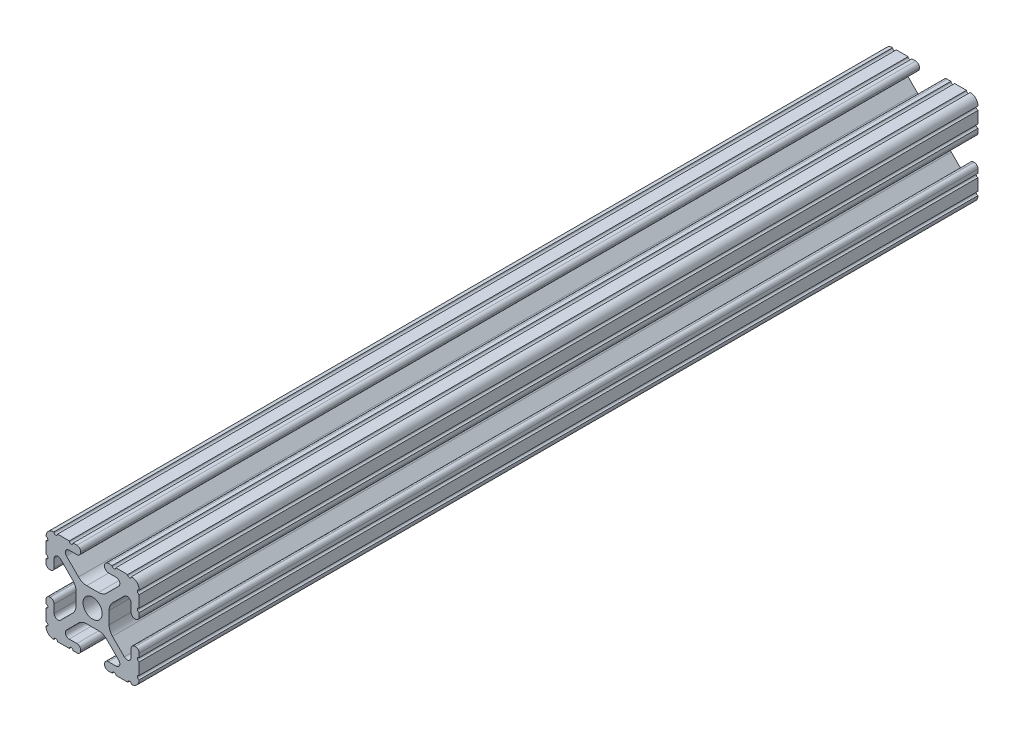
SolidWorks part; units mm, degrees
material "6061-T6 (SS)"
ref_plane "Front Plane" through (0, 0, 0) normal (0, 0, 1) x (1, 0, 0)
ref_plane "Top Plane" through (0, 0, 0) normal (0, 1, 0) x (1, 0, 0)
ref_plane "Right Plane" through (0, 0, 0) normal (1, 0, 0) x (0, 0, -1)
sketch "Sketch1" plane through (0, 0, 0) normal (0, 0, 1) x (0, 1, 0)
  line L0 (6.3331, -12.7) -> (9.5504, -12.7)
  line L1 (12.7, -9.5504) -> (12.7, -6.3331)
  line L2 (12.7, -5.3171) -> (12.7, -4.2875)
  line L3 (11.651, -3.2385) -> (11.5392, -3.2385)
  line L4 (10.4902, -4.2875) -> (10.4902, -6.4021)
  line L5 (8.7371, -7.1294) -> (5.441, -3.8408)
  line L6 (4.5085, -1.5932) -> (4.5085, 1.5932)
  line L7 (5.441, 3.8408) -> (8.7371, 7.1294)
  line L8 (10.4902, 6.4021) -> (10.4902, 4.2875)
  line L9 (11.5392, 3.2385) -> (11.651, 3.2385)
  line L10 (12.7, 4.2875) -> (12.7, 5.3171)
  line L11 (12.7, 6.3331) -> (12.7, 9.5504)
  line L12 (9.5504, 12.7) -> (6.3331, 12.7)
  line L13 (5.3171, 12.7) -> (4.2875, 12.7)
  line L14 (3.2385, 11.651) -> (3.2385, 11.5392)
  line L15 (4.2875, 10.4902) -> (6.4768, 10.4902)
  line L16 (7.207, 8.7244) -> (3.8983, 5.4232)
  line L17 (1.6558, 4.4958) -> (-1.6558, 4.4958)
  line L18 (-3.8983, 5.4232) -> (-7.207, 8.7244)
  line L19 (-6.4768, 10.4902) -> (-4.2875, 10.4902)
  line L20 (-3.2385, 11.5392) -> (-3.2385, 11.651)
  line L21 (-4.2875, 12.7) -> (-5.3171, 12.7)
  line L22 (-6.3331, 12.7) -> (-9.5504, 12.7)
  line L23 (-12.7, 9.5504) -> (-12.7, 6.3331)
  line L24 (-12.7, 5.3171) -> (-12.7, 4.2875)
  line L25 (-11.651, 3.2385) -> (-11.5392, 3.2385)
  line L26 (-10.4902, 4.2875) -> (-10.4902, 6.4021)
  line L27 (-8.7371, 7.1294) -> (-5.441, 3.8408)
  line L28 (-4.5085, 1.5932) -> (-4.5085, -1.5932)
  line L29 (-5.441, -3.8408) -> (-8.7371, -7.1294)
  line L30 (-10.4902, -6.4021) -> (-10.4902, -4.2875)
  line L31 (-11.5392, -3.2385) -> (-11.651, -3.2385)
  line L32 (-12.7, -4.2875) -> (-12.7, -5.3171)
  line L33 (-12.7, -6.3331) -> (-12.7, -9.5504)
  line L34 (-9.5504, -12.7) -> (-6.3331, -12.7)
  line L35 (-5.3171, -12.7) -> (-4.2875, -12.7)
  line L36 (-3.2385, -11.651) -> (-3.2385, -11.5392)
  line L37 (-4.2875, -10.4902) -> (-6.4164, -10.4902)
  line L38 (-7.1797, -8.6452) -> (-3.9523, -5.4237)
  line L39 (-1.7093, -4.4958) -> (1.7093, -4.4958)
  line L40 (3.9523, -5.4237) -> (7.1797, -8.6452)
  line L41 (6.4164, -10.4902) -> (4.2875, -10.4902)
  line L42 (3.2385, -11.5392) -> (3.2385, -11.651)
  line L43 (4.2875, -12.7) -> (5.3171, -12.7)
  circle A0 centre (0, 0) radius 2.6035
  arc A1 (6.3331, -12.7) -> (5.3171, -12.7) centre (5.8251, -12.7) ccw
  arc A2 (10.5664, -12.6998) -> (9.5504, -12.7) centre (10.0584, -12.7) ccw
  arc A3 (10.5664, -12.6998) -> (12.6998, -10.5664) centre (10.5918, -10.5918) ccw
  arc A4 (12.7, -9.5504) -> (12.6998, -10.5664) centre (12.7, -10.0584) ccw
  arc A5 (12.7, -5.3171) -> (12.7, -6.3331) centre (12.7, -5.8251) ccw
  arc A6 (12.7, -4.2875) -> (11.651, -3.2385) centre (11.651, -4.2875) ccw
  arc A7 (11.5392, -3.2385) -> (10.4902, -4.2875) centre (11.5392, -4.2875) ccw
  arc A8 (8.7371, -7.1294) -> (10.4902, -6.4021) centre (9.4628, -6.4021) ccw
  arc A9 (5.441, 3.8408) -> (4.5085, 1.5932) centre (7.6835, 1.5932) ccw
  arc A10 (10.4902, 6.4021) -> (8.7371, 7.1294) centre (9.4628, 6.4021) ccw
  arc A11 (10.4902, 4.2875) -> (11.5392, 3.2385) centre (11.5392, 4.2875) ccw
  arc A12 (11.651, 3.2385) -> (12.7, 4.2875) centre (11.651, 4.2875) ccw
  arc A13 (12.7, 6.3331) -> (12.7, 5.3171) centre (12.7, 5.8251) ccw
  arc A14 (12.6998, 10.5664) -> (12.7, 9.5504) centre (12.7, 10.0584) ccw
  arc A15 (12.6998, 10.5664) -> (10.5664, 12.6998) centre (10.5918, 10.5918) ccw
  arc A16 (9.5504, 12.7) -> (10.5664, 12.6998) centre (10.0584, 12.7) ccw
  arc A17 (5.3171, 12.7) -> (6.3331, 12.7) centre (5.8251, 12.7) ccw
  arc A18 (4.2875, 12.7) -> (3.2385, 11.651) centre (4.2875, 11.651) ccw
  arc A19 (3.2385, 11.5392) -> (4.2875, 10.4902) centre (4.2875, 11.5392) ccw
  arc A20 (7.207, 8.7244) -> (6.4768, 10.4902) centre (6.4768, 9.4563) ccw
  arc A21 (1.6558, 4.4958) -> (3.8983, 5.4232) centre (1.6558, 7.6708) ccw
  arc A22 (-3.8983, 5.4232) -> (-1.6558, 4.4958) centre (-1.6558, 7.6708) ccw
  arc A23 (-6.4768, 10.4902) -> (-7.207, 8.7244) centre (-6.4768, 9.4563) ccw
  arc A24 (-4.2875, 10.4902) -> (-3.2385, 11.5392) centre (-4.2875, 11.5392) ccw
  arc A25 (-3.2385, 11.651) -> (-4.2875, 12.7) centre (-4.2875, 11.651) ccw
  arc A26 (-6.3331, 12.7) -> (-5.3171, 12.7) centre (-5.8251, 12.7) ccw
  arc A27 (-10.5664, 12.6998) -> (-9.5504, 12.7) centre (-10.0584, 12.7) ccw
  arc A28 (-10.5664, 12.6998) -> (-12.6998, 10.5664) centre (-10.5918, 10.5918) ccw
  arc A29 (-12.7, 9.5504) -> (-12.6998, 10.5664) centre (-12.7, 10.0584) ccw
  arc A30 (-12.7, 5.3171) -> (-12.7, 6.3331) centre (-12.7, 5.8251) ccw
  arc A31 (-12.7, 4.2875) -> (-11.651, 3.2385) centre (-11.651, 4.2875) ccw
  arc A32 (-11.5392, 3.2385) -> (-10.4902, 4.2875) centre (-11.5392, 4.2875) ccw
  arc A33 (-8.7371, 7.1294) -> (-10.4902, 6.4021) centre (-9.4628, 6.4021) ccw
  arc A34 (-4.5085, 1.5932) -> (-5.441, 3.8408) centre (-7.6835, 1.5932) ccw
  arc A35 (-5.441, -3.8408) -> (-4.5085, -1.5932) centre (-7.6835, -1.5932) ccw
  arc A36 (-10.4902, -6.4021) -> (-8.7371, -7.1294) centre (-9.4628, -6.4021) ccw
  arc A37 (-10.4902, -4.2875) -> (-11.5392, -3.2385) centre (-11.5392, -4.2875) ccw
  arc A38 (-11.651, -3.2385) -> (-12.7, -4.2875) centre (-11.651, -4.2875) ccw
  arc A39 (-12.7, -6.3331) -> (-12.7, -5.3171) centre (-12.7, -5.8251) ccw
  arc A40 (-12.6998, -10.5664) -> (-12.7, -9.5504) centre (-12.7, -10.0584) ccw
  arc A41 (-12.6998, -10.5664) -> (-10.5664, -12.6998) centre (-10.5918, -10.5918) ccw
  arc A42 (-9.5504, -12.7) -> (-10.5664, -12.6998) centre (-10.0584, -12.7) ccw
  arc A43 (-5.3171, -12.7) -> (-6.3331, -12.7) centre (-5.8251, -12.7) ccw
  arc A44 (-4.2875, -12.7) -> (-3.2385, -11.651) centre (-4.2875, -11.651) ccw
  arc A45 (-3.2385, -11.5392) -> (-4.2875, -10.4902) centre (-4.2875, -11.5392) ccw
  arc A46 (-7.1797, -8.6452) -> (-6.4164, -10.4902) centre (-6.4164, -9.4098) ccw
  arc A47 (-1.7093, -4.4958) -> (-3.9523, -5.4237) centre (-1.7093, -7.6708) ccw
  arc A48 (3.9523, -5.4237) -> (1.7093, -4.4958) centre (1.7093, -7.6708) ccw
  arc A49 (6.4164, -10.4902) -> (7.1797, -8.6452) centre (6.4164, -9.4098) ccw
  arc A50 (4.2875, -10.4902) -> (3.2385, -11.5392) centre (4.2875, -11.5392) ccw
  arc A51 (3.2385, -11.651) -> (4.2875, -12.7) centre (4.2875, -11.651) ccw
  arc A52 (5.441, -3.8408) -> (4.5085, -1.5932) centre (7.6835, -1.5932) cw
  dimension "D1" = 3.175
extrude "Boss-Extrude1" add sketch "Sketch1" along normal mid plane 228.6
